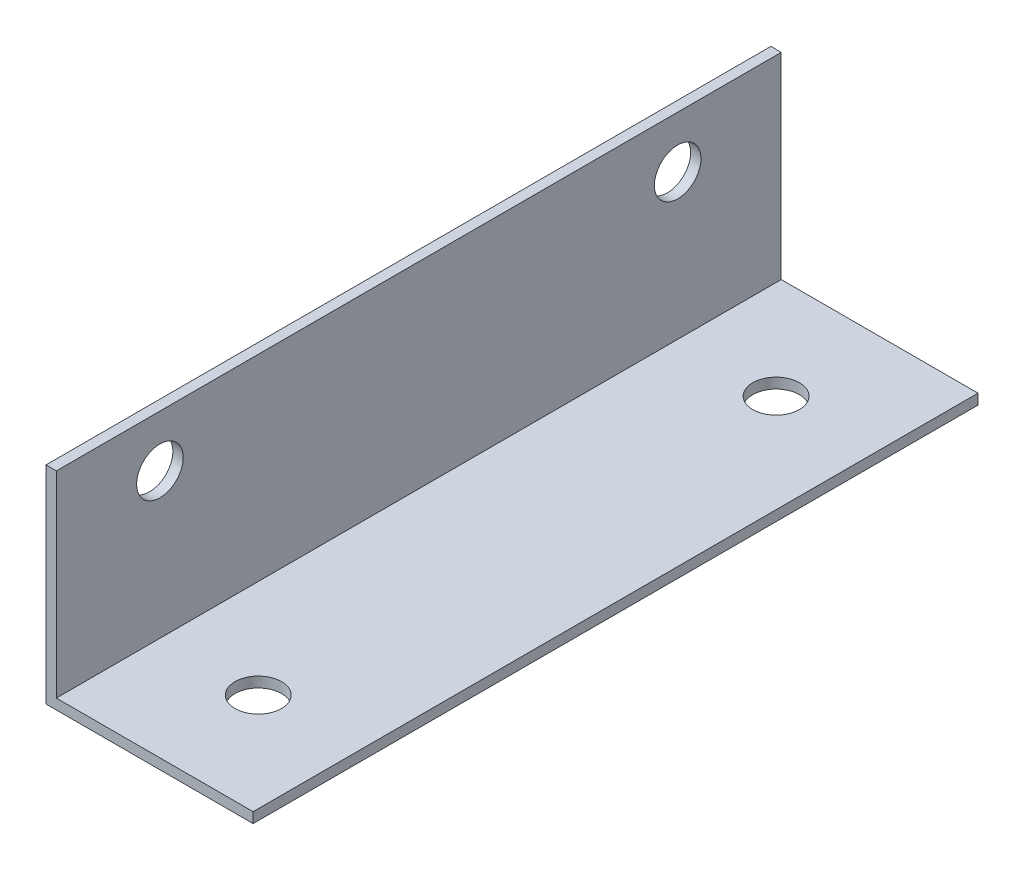
SolidWorks part; units mm, degrees
ref_plane "Спереди" through (0, 0, 0) normal (0, 0, 1) x (1, 0, 0)
ref_plane "Сверху" through (0, 0, 0) normal (0, 1, 0) x (1, 0, 0)
ref_plane "Справа" through (0, 0, 0) normal (1, 0, 0) x (0, 0, -1)
sketch "Эскиз1" plane through (0, 0, 0) normal (0, 0, 1) x (1, 0, 0)
  line L0 (0, 0) -> (0, 20)
  line L1 (0, 20) -> (1, 20)
  line L2 (1, 20) -> (1, 1)
  line L3 (1, 1) -> (20, 1)
  line L4 (20, 1) -> (20, 0)
  line L5 (20, 0) -> (0, 0)
  dimension "D1" = 20
  dimension "D2" = 1
extrude "Бобышка-Вытянуть1" add sketch "Эскиз1" along normal blind 70
sketch "Эскиз2" plane through (0, 1, 0) normal (0, 1, 0) x (1, 0, 0)
  line L0 (10.5, 0) -> (10.5, -70) construction
  line L1 (20, 0) -> (1, 0) construction
  line L2 (20, -70) -> (1, -70) construction
  line L3 (1, -35) -> (20, -35) construction
  line L4 (1, -70) -> (1, 0) construction
  line L5 (20, -70) -> (20, 0) construction
  circle A0 centre (10.5, -10) radius 2.25
  circle A1 centre (10.5, -60) radius 2.25
  dimension "D1" = 25
  dimension "D2" = 4.5
  dimension "D3" = 50
extrude "Вырез-Вытянуть1" cut sketch "Эскиз2" against normal through all
sketch "Эскиз3" plane through (1, 0, 0) normal (1, 0, 0) x (0, 0, -1)
  line L0 (0, 15) -> (-70, 15) construction
  line L1 (0, 1) -> (0, 20) construction
  line L2 (-70, 1) -> (-70, 20) construction
  line L3 (-70, 20) -> (0, 20) construction
  circle A0 centre (-10, 15) radius 2.25
  circle A1 centre (-60, 15) radius 2.25
  dimension "D2" = 10
  dimension "D3" = 4.5
  dimension "D1" = 10
  dimension "D4" = 5
extrude "Вырез-Вытянуть2" cut sketch "Эскиз3" against normal through all
